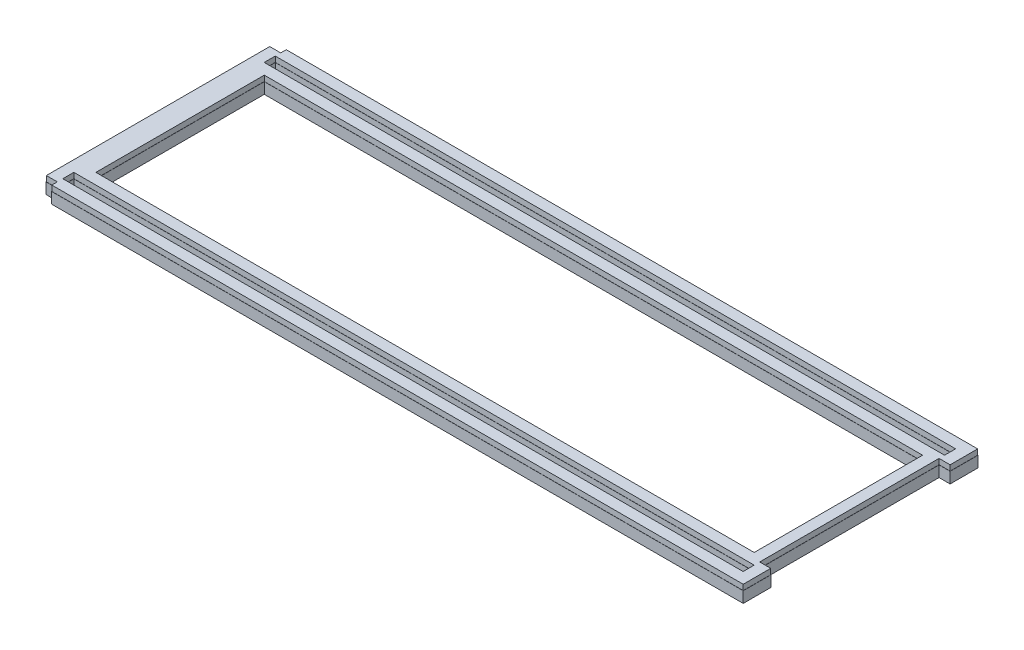
SolidWorks part; units mm, degrees
ref_plane "Front" through (0, 0, 0) normal (0, 0, 1) x (1, 0, 0)
ref_plane "Top" through (0, 0, 0) normal (0, 1, 0) x (1, 0, 0)
ref_plane "Right" through (0, 0, 0) normal (1, 0, 0) x (0, 0, -1)
sketch "Sketch1" plane through (0, 0, 0) normal (0, 1, 0) x (1, 0, 0)
  line L0 (-203.2, 64.6208) -> (-203.2, -64.6208)
  line L1 (-196.85, 67.8212) -> (203.2, 67.8212)
  line L3 (-196.85, -67.8212) -> (203.2, -67.8212)
  line L4 (203.2, 67.8212) -> (203.2, 51.8954)
  line L5 (0, 0) -> (-84.4016, 0) construction
  line L7 (-196.85, 61.4712) -> (196.7992, 61.4712)
  line L9 (-196.85, 55.0704) -> (196.7992, 55.0704)
  line L10 (196.7992, 61.4712) -> (196.7992, 55.0704)
  line L11 (-196.85, -55.0704) -> (196.7992, -55.0704)
  line L13 (-196.85, -61.4712) -> (196.7992, -61.4712)
  line L14 (196.7992, -55.0704) -> (196.7992, -61.4712)
  line L16 (203.2, -51.8954) -> (203.2, -67.8212)
  line L17 (203.2, 51.8954) -> (196.7992, 51.8954)
  line L19 (203.2, -51.8954) -> (196.7992, -51.8954)
  line L20 (196.7992, 51.8954) -> (196.7992, -51.8954)
  line L32 (0, -24.3249) -> (0, 0) construction
  line L37 (-196.85, -55.0704) -> (-196.85, -61.4712)
  line L41 (-196.85, 55.0704) -> (-196.85, 61.4712)
  line L48 (-203.2, -64.6208) -> (-196.85, -64.6208)
  line L49 (-196.85, -67.8212) -> (-196.85, -64.6208)
  line L50 (-203.2, 64.6208) -> (-196.85, 64.6208)
  line L53 (-196.85, 64.6208) -> (-196.85, 67.8212)
  line L54 (-190.4492, 48.7204) -> (190.4492, 48.7204)
  line L55 (-190.4492, 48.7204) -> (-190.4492, -48.7204)
  line L56 (-190.4492, -48.7204) -> (190.4492, -48.7204)
  line L57 (190.4492, 48.7204) -> (190.4492, -48.7204)
  line L58 (-190.4492, 48.7204) -> (190.4492, -48.7204) construction
  line L59 (-190.4492, -48.7204) -> (190.4492, 48.7204) construction
  point P0 (0, 0)
  point P12 (0, 0)
  dimension "D1" = 135.6423
  dimension "D3" = 6.4008
  dimension "D4" = 6.35
  dimension "D5" = 6.35
  dimension "D6" = 6.4008
  dimension "D7" = 3.175
  dimension "D8" = 3.175
  dimension "D2" = 406.4
  dimension "D10" = 67.8212
  dimension "D11" = 203.2
  dimension "D9" = 393.6492
  dimension "D12" = 3.2004
  dimension "D13" = 3.2004
  dimension "D14" = 6.35
  dimension "D15" = 6.35
extrude "Boss-Extrude1" add sketch "Sketch1" along normal blind 3.175
ref_plane "Plane1" [suppressed] through (0, 0, 0) normal (0, -1, 0) x (-1, 0, 0)
sketch "Sketch3" [suppressed] plane through (0, 0, 0) normal (0, -1, 0) x (-1, 0, 0)
  line L24 (-203.3016, -42.6561) -> (-203.3016, -58.7851)
  line L25 (-203.3016, -58.7851) -> (196.9516, -58.7851)
  line L26 (196.9516, -58.7851) -> (196.9516, -55.5847)
  line L27 (196.9516, -55.5847) -> (203.3016, -55.5847)
  line L28 (203.3016, -55.5847) -> (203.3016, 55.5847)
  line L29 (203.3016, 55.5847) -> (196.9516, 55.5847)
  line L30 (196.9516, 55.5847) -> (196.9516, 58.7851)
  line L31 (196.9516, 58.7851) -> (-203.3016, 58.7851)
  line L32 (-203.3016, 58.7851) -> (-203.3016, 42.6561)
  line L33 (-203.3016, 42.6561) -> (-196.9008, 42.6561)
  line L34 (-196.9008, 42.6561) -> (-196.9008, -42.6561)
  line L35 (-196.9008, -42.6561) -> (-203.3016, -42.6561)
  line L36 (-203.3016, -42.6561) -> (-203.3016, -58.7851)
  line L37 (-203.3016, -58.7851) -> (196.9516, -58.7851)
  line L38 (196.9516, -58.7851) -> (196.9516, -55.5847)
  line L39 (196.9516, -55.5847) -> (203.3016, -55.5847)
  line L40 (203.3016, -55.5847) -> (203.3016, 55.5847)
  line L41 (203.3016, 55.5847) -> (196.9516, 55.5847)
  line L42 (196.9516, 55.5847) -> (196.9516, 58.7851)
  line L43 (196.9516, 58.7851) -> (-203.3016, 58.7851)
  line L44 (-203.3016, 58.7851) -> (-203.3016, 42.6561)
  line L45 (-203.3016, 42.6561) -> (-196.9008, 42.6561)
  line L46 (-196.9008, 42.6561) -> (-196.9008, -42.6561)
  line L47 (-196.9008, -42.6561) -> (-203.3016, -42.6561)
  line L51 (-196.6976, 52.2319) -> (-196.6976, 46.0343)
  line L52 (-196.6976, 46.0343) -> (196.7484, 46.0343)
  line L53 (196.7484, 46.0343) -> (196.7484, 52.2319)
  line L54 (196.7484, 52.2319) -> (-196.6976, 52.2319)
  line L55 (-196.6976, 52.2319) -> (-196.6976, 46.0343)
  line L56 (-196.6976, 46.0343) -> (196.7484, 46.0343)
  line L57 (196.7484, 46.0343) -> (196.7484, 52.2319)
  line L58 (196.7484, 52.2319) -> (-196.6976, 52.2319)
  line L69 (190.3476, -39.4811) -> (190.3476, 39.4811)
  line L70 (-190.3476, -39.4811) -> (190.3476, -39.4811)
  line L71 (190.3476, 39.4811) -> (-190.3476, 39.4811)
  line L72 (-190.3476, 39.4811) -> (-190.3476, -39.4811)
  line L73 (190.3476, -39.4811) -> (190.3476, 39.4811)
  line L74 (-190.3476, -39.4811) -> (190.3476, -39.4811)
  line L75 (190.3476, 39.4811) -> (-190.3476, 39.4811)
  line L76 (-190.3476, 39.4811) -> (-190.3476, -39.4811)
  line L87 (-196.6976, -46.0343) -> (-196.6976, -52.2319)
  line L88 (-196.6976, -52.2319) -> (196.7484, -52.2319)
  line L89 (196.7484, -52.2319) -> (196.7484, -46.0343)
  line L90 (196.7484, -46.0343) -> (-196.6976, -46.0343)
  line L91 (-196.6976, -46.0343) -> (-196.6976, -52.2319)
  line L92 (-196.6976, -52.2319) -> (196.7484, -52.2319)
  line L93 (196.7484, -52.2319) -> (196.7484, -46.0343)
  line L94 (196.7484, -46.0343) -> (-196.6976, -46.0343)
  dimension "D1" = 0.1016
  dimension "D2" = 0.1016
  dimension "D3" = 0.1016
  dimension "D4" = 0.1016
extrude "Boss-Extrude2" [suppressed] add sketch "Sketch3" along normal blind 6.35
ref_plane "Plane2" [suppressed] through (0, 0, 0) normal (0, -1, 0) x (-1, 0, 0)
sketch "Sketch4" [suppressed] plane through (0, 0, 0) normal (0, -1, 0) x (-1, 0, 0)
  line L24 (-203.3016, -47.2249) -> (-203.3016, -63.3539)
  line L25 (-203.3016, -63.3539) -> (196.9516, -63.3539)
  line L26 (196.9516, -63.3539) -> (196.9516, -60.1535)
  line L27 (196.9516, -60.1535) -> (203.3016, -60.1535)
  line L28 (203.3016, -60.1535) -> (203.3016, 60.1536)
  line L29 (203.3016, 60.1536) -> (196.9516, 60.1536)
  line L30 (196.9516, 60.1536) -> (196.9516, 63.354)
  line L31 (196.9516, 63.354) -> (-203.3016, 63.354)
  line L32 (-203.3016, 63.354) -> (-203.3016, 47.225)
  line L33 (-203.3016, 47.225) -> (-196.9008, 47.225)
  line L34 (-196.9008, 47.225) -> (-196.9008, -47.2249)
  line L35 (-196.9008, -47.2249) -> (-203.3016, -47.2249)
  line L36 (-203.3016, -47.2249) -> (-203.3016, -63.3539)
  line L37 (-203.3016, -63.3539) -> (196.9516, -63.3539)
  line L38 (196.9516, -63.3539) -> (196.9516, -60.1535)
  line L39 (196.9516, -60.1535) -> (203.3016, -60.1535)
  line L40 (203.3016, -60.1535) -> (203.3016, 60.1536)
  line L41 (203.3016, 60.1536) -> (196.9516, 60.1536)
  line L42 (196.9516, 60.1536) -> (196.9516, 63.354)
  line L43 (196.9516, 63.354) -> (-203.3016, 63.354)
  line L44 (-203.3016, 63.354) -> (-203.3016, 47.225)
  line L45 (-203.3016, 47.225) -> (-196.9008, 47.225)
  line L46 (-196.9008, 47.225) -> (-196.9008, -47.2249)
  line L47 (-196.9008, -47.2249) -> (-203.3016, -47.2249)
  line L50 (196.7484, 50.6032) -> (196.7484, 56.8008)
  line L51 (-196.6976, 50.6032) -> (196.7484, 50.6032)
  line L52 (-196.6976, 56.8008) -> (-196.6976, 50.6032)
  line L53 (196.7484, 56.8008) -> (-196.6976, 56.8008)
  line L54 (196.7484, 50.6032) -> (196.7484, 56.8008)
  line L55 (-196.6976, 50.6032) -> (196.7484, 50.6032)
  line L56 (-196.6976, 56.8008) -> (-196.6976, 50.6032)
  line L57 (196.7484, 56.8008) -> (-196.6976, 56.8008)
  line L68 (-190.3476, 44.0499) -> (-190.3476, -44.0499)
  line L69 (-190.3476, -44.0499) -> (190.3476, -44.0499)
  line L70 (190.3476, -44.0499) -> (190.3476, 44.0499)
  line L71 (190.3476, 44.0499) -> (-190.3476, 44.0499)
  line L72 (-190.3476, 44.0499) -> (-190.3476, -44.0499)
  line L73 (-190.3476, -44.0499) -> (190.3476, -44.0499)
  line L74 (190.3476, -44.0499) -> (190.3476, 44.0499)
  line L75 (190.3476, 44.0499) -> (-190.3476, 44.0499)
  line L86 (-196.6976, -50.6031) -> (-196.6976, -56.8008)
  line L87 (-196.6976, -56.8008) -> (196.7484, -56.8008)
  line L88 (196.7484, -56.8008) -> (196.7484, -50.6031)
  line L89 (196.7484, -50.6031) -> (-196.6976, -50.6031)
  line L90 (-196.6976, -50.6031) -> (-196.6976, -56.8008)
  line L91 (-196.6976, -56.8008) -> (196.7484, -56.8008)
  line L92 (196.7484, -56.8008) -> (196.7484, -50.6031)
  line L93 (196.7484, -50.6031) -> (-196.6976, -50.6031)
  dimension "D1" = 0.1016
  dimension "D2" = 0.1016
  dimension "D3" = 0.1016
  dimension "D4" = 0.1016
extrude "Boss-Extrude3" [suppressed] add sketch "Sketch4" along normal blind 6.35
ref_plane "Plane3" through (0, 0, 0) normal (0, -1, 0) x (-1, 0, 0)
sketch "Sketch5" plane through (0, 0, 0) normal (0, -1, 0) x (-1, 0, 0)
  line L36 (-203.3016, -51.7938) -> (-203.3016, -67.9228)
  line L37 (-203.3016, -67.9228) -> (196.9516, -67.9228)
  line L38 (196.9516, -67.9228) -> (196.9516, -64.7224)
  line L39 (196.9516, -64.7224) -> (203.3016, -64.7224)
  line L40 (203.3016, -64.7224) -> (203.3016, 64.7224)
  line L41 (203.3016, 64.7224) -> (196.9516, 64.7224)
  line L42 (196.9516, 64.7224) -> (196.9516, 67.9228)
  line L43 (196.9516, 67.9228) -> (-203.3016, 67.9228)
  line L44 (-203.3016, 67.9228) -> (-203.3016, 51.7938)
  line L45 (-203.3016, 51.7938) -> (-196.9008, 51.7938)
  line L46 (-196.9008, 51.7938) -> (-196.9008, -51.7938)
  line L47 (-196.9008, -51.7938) -> (-203.3016, -51.7938)
  line L48 (-203.3016, -51.7938) -> (-203.3016, -67.9228)
  line L49 (-203.3016, -67.9228) -> (196.9516, -67.9228)
  line L50 (196.9516, -67.9228) -> (196.9516, -64.7224)
  line L51 (196.9516, -64.7224) -> (203.3016, -64.7224)
  line L52 (203.3016, -64.7224) -> (203.3016, 64.7224)
  line L53 (203.3016, 64.7224) -> (196.9516, 64.7224)
  line L54 (196.9516, 64.7224) -> (196.9516, 67.9228)
  line L55 (196.9516, 67.9228) -> (-203.3016, 67.9228)
  line L56 (-203.3016, 67.9228) -> (-203.3016, 51.7938)
  line L57 (-203.3016, 51.7938) -> (-196.9008, 51.7938)
  line L58 (-196.9008, 51.7938) -> (-196.9008, -51.7938)
  line L59 (-196.9008, -51.7938) -> (-203.3016, -51.7938)
  line L62 (196.7484, 55.172) -> (196.7484, 61.3696)
  line L63 (-196.6976, 55.172) -> (196.7484, 55.172)
  line L64 (196.7484, 61.3696) -> (-196.6976, 61.3696)
  line L65 (-196.6976, 61.3696) -> (-196.6976, 55.172)
  line L66 (196.7484, 55.172) -> (196.7484, 61.3696)
  line L67 (-196.6976, 55.172) -> (196.7484, 55.172)
  line L68 (196.7484, 61.3696) -> (-196.6976, 61.3696)
  line L69 (-196.6976, 61.3696) -> (-196.6976, 55.172)
  line L80 (-190.3476, 48.6188) -> (-190.3476, -48.6188)
  line L81 (-190.3476, -48.6188) -> (190.3476, -48.6188)
  line L82 (190.3476, -48.6188) -> (190.3476, 48.6188)
  line L83 (190.3476, 48.6188) -> (-190.3476, 48.6188)
  line L84 (-190.3476, 48.6188) -> (-190.3476, -48.6188)
  line L85 (-190.3476, -48.6188) -> (190.3476, -48.6188)
  line L86 (190.3476, -48.6188) -> (190.3476, 48.6188)
  line L87 (190.3476, 48.6188) -> (-190.3476, 48.6188)
  line L101 (196.7484, -61.3696) -> (196.7484, -55.172)
  line L102 (-196.6976, -61.3696) -> (196.7484, -61.3696)
  line L103 (-196.6976, -55.172) -> (-196.6976, -61.3696)
  line L104 (196.7484, -55.172) -> (-196.6976, -55.172)
  line L105 (196.7484, -61.3696) -> (196.7484, -55.172)
  line L106 (-196.6976, -61.3696) -> (196.7484, -61.3696)
  line L107 (-196.6976, -55.172) -> (-196.6976, -61.3696)
  line L108 (196.7484, -55.172) -> (-196.6976, -55.172)
  dimension "D1" = 0.1016
  dimension "D2" = 0.1016
  dimension "D3" = 0.1016
  dimension "D4" = 0.1016
extrude "Boss-Extrude4" add sketch "Sketch5" along normal blind 6.35
equation "\"D1@Sketch1\"        = (5.59025-.25)"
equation "\"D10@Sketch1\"=\"D1@Sketch1\"/2"
